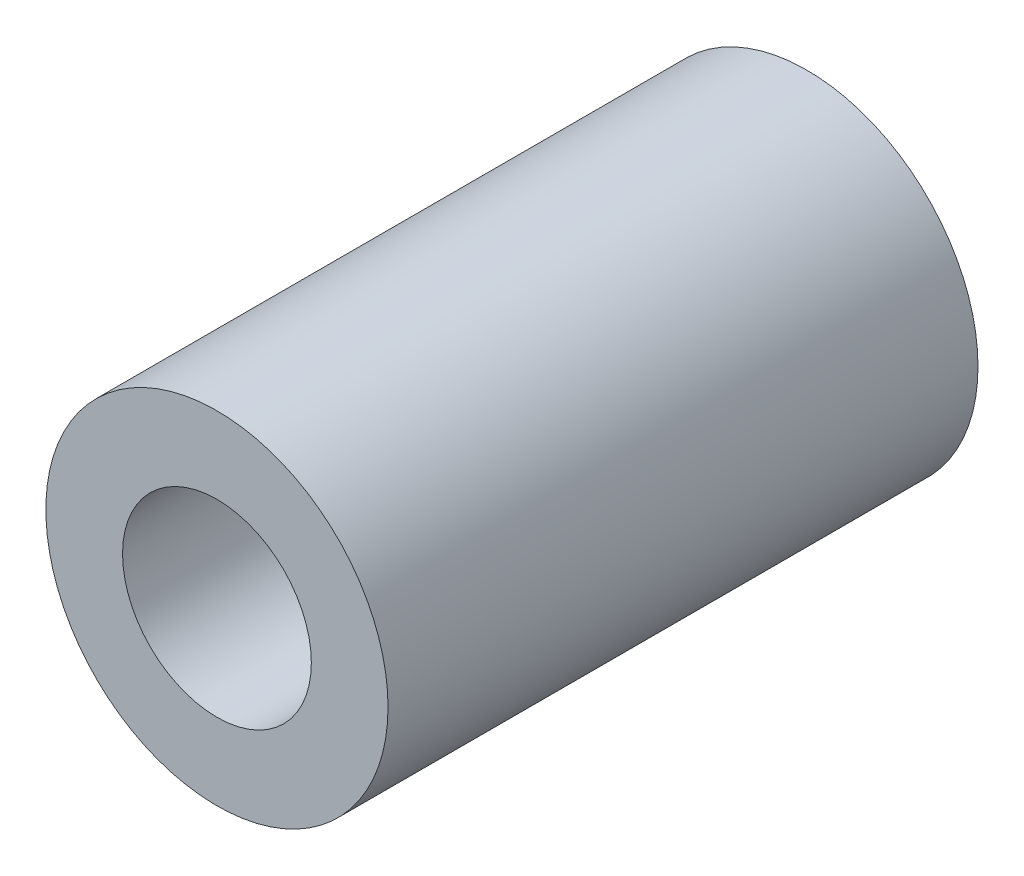
SolidWorks part; units mm, degrees
ref_plane "Front Plane" through (0, 0, 0) normal (0, 0, 1) x (1, 0, 0)
ref_plane "Top Plane" through (0, 0, 0) normal (0, 1, 0) x (1, 0, 0)
ref_plane "Right Plane" through (0, 0, 0) normal (1, 0, 0) x (0, 0, -1)
sketch "Sketch1" plane through (0, 0, 0) normal (0, 0, 1) x (1, 0, 0)
  circle A0 centre (0, 0) radius 1.6
  circle A1 centre (0, 0) radius 2.9
  dimension "D1" = 3.2
  dimension "D2" = 5.8
extrude "Boss-Extrude1" add sketch "Sketch1" along normal blind 10
